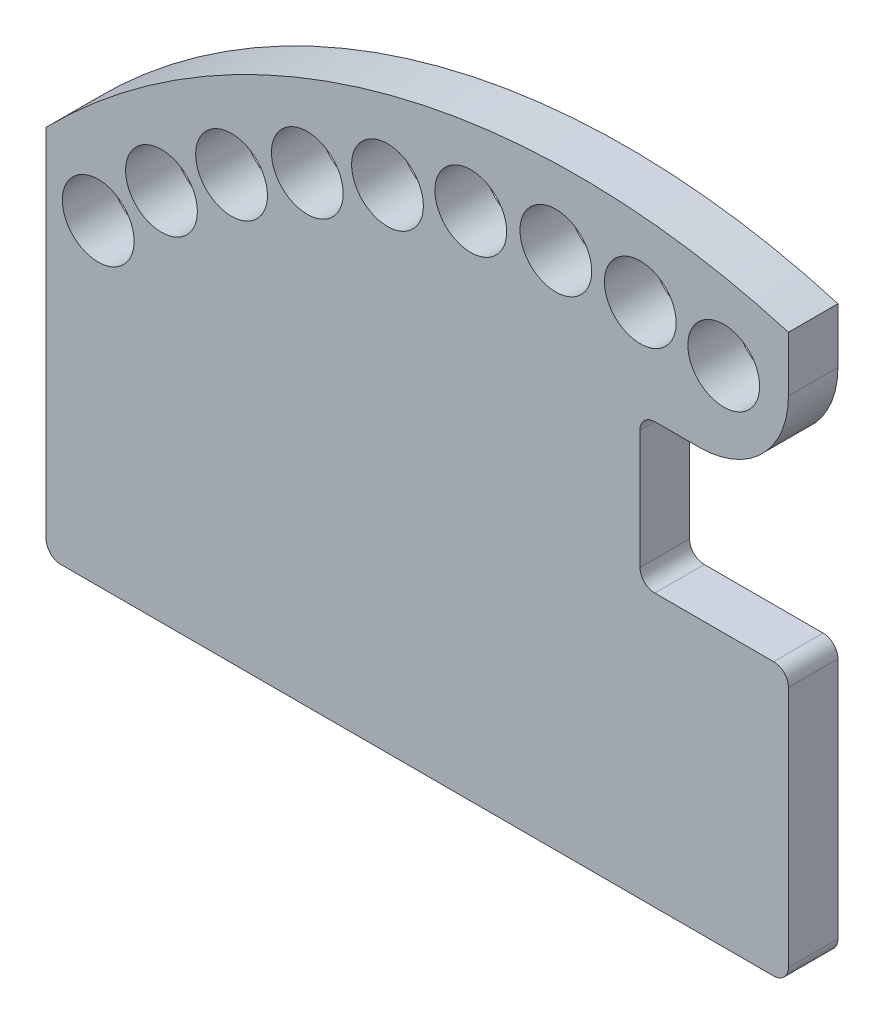
SolidWorks part; units mm, degrees
ref_plane "Plan de face" through (0, 0, 0) normal (0, 0, 1) x (1, 0, 0)
ref_plane "Plan de dessus" through (0, 0, 0) normal (0, 1, 0) x (1, 0, 0)
ref_plane "Plan de droite" through (0, 0, 0) normal (1, 0, 0) x (0, 0, -1)
sketch "Esquisse3" plane through (0, 0, 0) normal (0, 0, 1) x (1, 0, 0)
  circle A0 centre (32.5, -30) radius 135
sketch "Esquisse1" plane through (0, 0, 0) normal (0, 0, 1) x (1, 0, 0)
  line L0 (75, 0) -> (-75, 0)
  line L1 (-75, 0) -> (-75, 75)
  line L2 (75, 0) -> (75, 114.1354)
  arc A0 (-75, 75) -> (75, 114.1354) centre (32.5, -30) cw
  point P6 (0, 0)
  dimension "D1" = 75
  dimension "D4" = 150
extrude "Boss.-Extru.1" add sketch "Esquisse1" along normal blind 10
sketch "Esquisse2" plane through (0, 0, 10) normal (0, 0, 1) x (1, 0, 0)
  circle A0 centre (32.5, -30) radius 135 construction
  circle A1 centre (28, 104.925) radius 7.25
  dimension "D1" = 28
  dimension "D2" = 14.5
extrude "Enlèv. mat.-Extru.1" cut sketch "Esquisse2" against normal through all
pattern_circular "Répétition circulaire1" count 7 over 44 about axis through (32.5, -30, 0) along (0, 0, 1) of "Enlèv. mat.-Extru.1"
sketch "Esquisse4" plane through (0, 0, 10) normal (0, 0, 1) x (1, 0, 0)
  circle A0 centre (32.5, -30) radius 135
pattern_circular "Répétition circulaire2" count 3 over 14.5 about axis through (32.5, -30, 0) along (0, 0, 1) of "Enlèv. mat.-Extru.1"
sketch "Esquisse5" plane through (0, 0, 10) normal (0, 0, 1) x (1, 0, 0)
  line L0 (75, 85) -> (45, 85)
  line L1 (75, 0) -> (75, 114.1354) construction
  line L2 (45, 85) -> (45, 55)
  line L3 (45, 55) -> (75, 55)
  line L4 (75, 55) -> (75, 85)
  line L5 (-75, 0) -> (75, 0) construction
  dimension "D1" = 30
  dimension "D2" = 30
  dimension "D3" = 55
extrude "Enlèv. mat.-Extru.2" cut sketch "Esquisse5" against normal blind 10
fillet "Congé1" radius 18 1 edges at (75, 85, 5)
fillet "Congé2" radius 3 5 edges at (-75, 0, 5) (75, 0, 5) (75, 55, 5) (45, 55, 5) (45, 85, 5)
equation "\"D1@Esquisse3\"=122.5-20-70"
